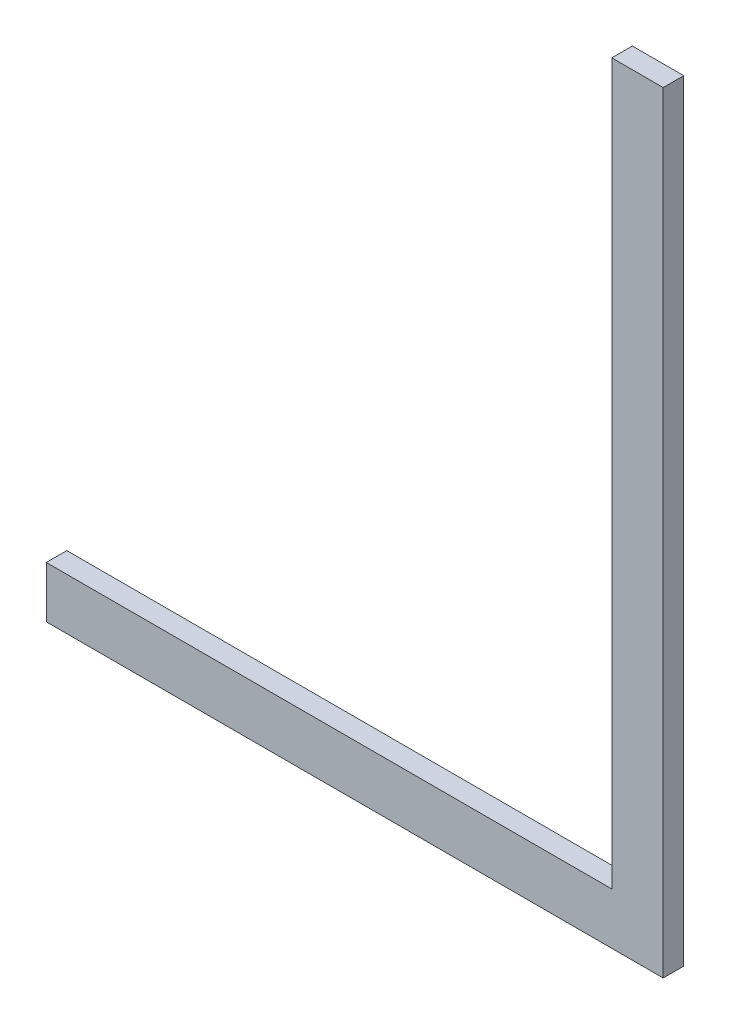
SolidWorks part; units mm, degrees
ref_plane "前视基准面" through (0, 0, 0) normal (0, 0, 1) x (1, 0, 0)
ref_plane "上视基准面" through (0, 0, 0) normal (0, 1, 0) x (1, 0, 0)
ref_plane "右视基准面" through (0, 0, 0) normal (1, 0, 0) x (0, 0, -1)
sketch "草图1" plane through (0, 0, 0) normal (0, 0, 1) x (1, 0, 0)
  line L1 (4.1216, 145.4561) -> (-5.8784, 145.4561)
  line L2 (4.1216, 145.4561) -> (4.1216, -4.5439)
  line L3 (4.1216, -4.5439) -> (-5.8784, -4.5439)
  line L4 (-5.8784, 145.4561) -> (-5.8784, -4.5439)
  line L5 (4.1216, 145.4561) -> (-5.8784, -4.5439) construction
  line L6 (4.1216, -4.5439) -> (-5.8784, 145.4561) construction
  point P0 (-0.8784, 70.4561)
  dimension "D1" = 150
  dimension "D2" = 10
extrude "凸台-拉伸1" add sketch "草图1" along normal blind 4
sketch "草图2" plane through (0, 0, 4) normal (0, 0, 1) x (1, 0, 0)
  line L0 (-5.8784, -4.5439) -> (-115.8784, -4.5439)
  line L1 (-115.8784, -4.5439) -> (-115.8784, 5.4561)
  line L2 (-115.8784, 5.4561) -> (-5.8784, 5.4561)
  line L3 (-5.8784, 145.4561) -> (-5.8784, -4.5439) construction
  line L4 (-5.8784, 5.4561) -> (-5.8784, -4.5439)
  dimension "D1" = 10
  dimension "D2" = 110
extrude "凸台-拉伸2" add sketch "草图2" against normal blind 4
sketch "草图3" plane through (0, 0, 0) normal (0, 0, -1) x (-1, 0, 0)
  line L0 (0.8784, 145.4561) -> (0.8784, 141.7561) construction
  line L1 (-4.1216, 145.4561) -> (5.8784, 145.4561) construction
  circle A0 centre (0.8784, 135.4561) radius 3
  point P6 (0, 0)
  dimension "D1" = 10
extrude "凸台-拉伸3" add sketch "草图3" along normal blind 1
